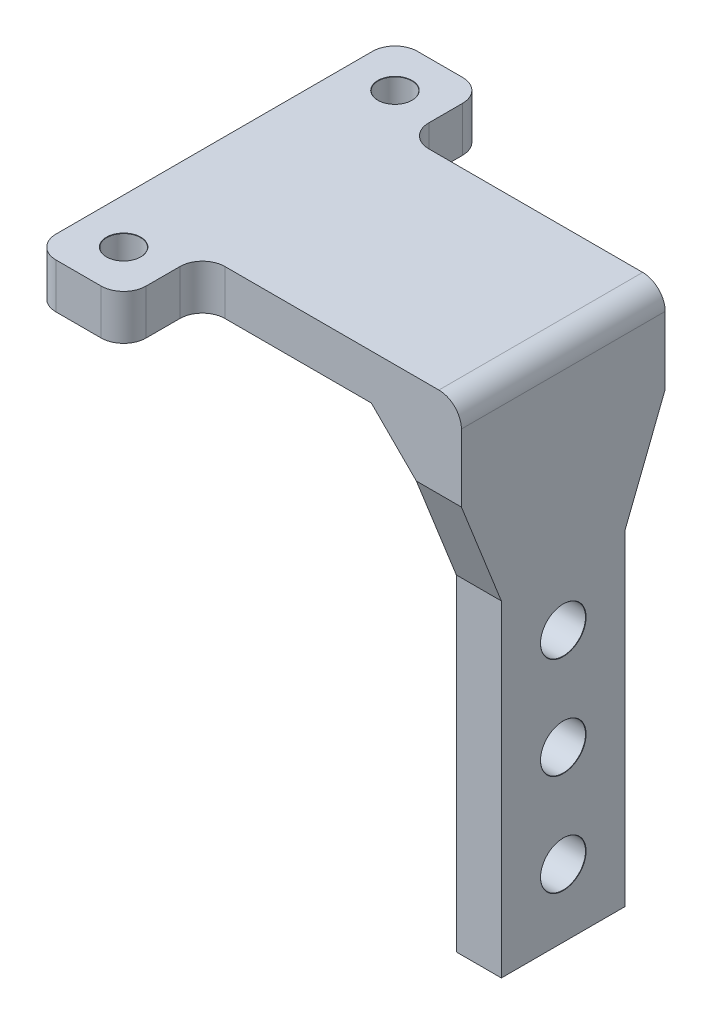
SolidWorks part; units mm, degrees
material "ABS"
ref_plane "Front Plane" through (0, 0, 0) normal (0, 0, 1) x (1, 0, 0)
ref_plane "Top Plane" through (0, 0, 0) normal (0, 1, 0) x (1, 0, 0)
ref_plane "Right Plane" through (0, 0, 0) normal (1, 0, 0) x (0, 0, -1)
sketch "Sketch1" plane through (0, 0, 0) normal (0, 1, 0) x (1, 0, 0)
  line L0 (0, 16.05) -> (0, -16.05)
  line L1 (0, -16.05) -> (8, -16.05)
  line L2 (8, -16.05) -> (8, -9.05)
  line L3 (8, -9.05) -> (31, -9.05)
  line L4 (31, -9.05) -> (31, 9.05)
  line L5 (31, 9.05) -> (8, 9.05)
  line L6 (8, 9.05) -> (8, 16.05)
  line L7 (8, 16.05) -> (0, 16.05)
  dimension "D1" = 32.1
  dimension "D2" = 8
  dimension "D3" = 7
  dimension "D4" = 23
extrude "Boss-Extrude1" add sketch "Sketch1" along normal blind 4
fillet "Fillet1" radius 2 6 edges at (0, 2, -16.05) (8, 2, -9.05) (8, 2, -16.05) (0, 2, 16.05) (8, 2, 16.05) (8, 2, 9.05)
hole_wizard "Ø3.0mm Dowel Hole1" positions "Sketch2" profile "Sketch3" hole size "Ø3.0" standard "ANSI Metric" end condition through all
sketch "Sketch2" plane through (0, 4, 0) normal (0, 1, 0) x (1, 0, 0)
  line L0 (4, 14.9464) -> (4, 9.6271) construction
  line L2 (0, 14.05) -> (0, -14.05) construction
  line L3 (8, 11.05) -> (8, 14.05) construction
  line L4 (6, 16.05) -> (2, 16.05) construction
  line L5 (2, -16.05) -> (6, -16.05) construction
  point P0 (4, 12.05)
  point P2 (4, -12.05)
  dimension "D1" = 4
  dimension "D2" = 4
sketch "Sketch3" plane through (4, 4, -12.05) normal (1, 0, 0) x (0, 0, 1)
  line L0 (0, 0) -> (0, 4)
  line L1 (0, 4) -> (1.5, 4)
  line L2 (1.5, 4) -> (1.5, 0.025)
  line L3 (1.5, 0.025) -> (1.525, 0)
  line L5 (1.525, 0) -> (0, 0)
  line L6 (-1.5, 0.025) -> (-1.525, 0) construction
  line L11 (0, -6.35) -> (0, 107.95) construction
  dimension "Thru Hole Dia." = 3
  dimension "Thru Hole Depth" = 4
  dimension "Near C'Sink Dia." = 3.05
  dimension "Near C'Sink Angle" = 90
sketch "Sketch4" plane through (0, 0, 0) normal (0, -1, 0) x (-1, 0, 0)
  line L0 (-31, 9.05) -> (-10, 9.05) construction
  line L1 (-31, -9.05) -> (-27, -9.05)
  line L2 (-31, -9.05) -> (-31, 9.05)
  line L3 (-31, 9.05) -> (-27, 9.05)
  line L4 (-27, -9.05) -> (-27, 9.05)
  dimension "D1" = 4
extrude "Boss-Extrude2" add sketch "Sketch4" along normal blind 42
chamfer "Chamfer1" distance 4 angle 45 1 edges at (27, 0, 0)
fillet "Fillet2" radius 2 1 edges at (31, 4, 0)
hole_wizard "Ø4.0mm Dowel Hole1" positions "Sketch7" profile "Sketch9" hole size "Ø4.0" standard "ANSI Metric" end condition through all
sketch "Sketch7" plane through (31, 0, 0) normal (1, 0, 0) x (0, 0, -1)
  line L0 (0, -29.3755) -> (0, -38.7068) construction
  line L2 (-9.05, 2) -> (-9.05, -42) construction
  line L3 (9.05, 2) -> (9.05, -42) construction
  line L4 (9.05, -42) -> (-9.05, -42) construction
  point P0 (0, -36)
  point P2 (0, -27)
  point P4 (0, -18)
  dimension "D1" = 6
  dimension "D2" = 9
  dimension "D3" = 9
sketch "Sketch9" plane through (31, -36, 0) normal (0, 1, 0) x (0, 0, -1)
  line L0 (0, 0) -> (0, 31)
  line L1 (0, 31) -> (2, 31)
  line L2 (2, 31) -> (2, 0.025)
  line L3 (2, 0.025) -> (2.025, 0)
  line L5 (2.025, 0) -> (0, 0)
  line L6 (-2, 0.025) -> (-2.025, 0) construction
  line L11 (0, -6.35) -> (0, 107.95) construction
  dimension "Thru Hole Dia." = 4
  dimension "Thru Hole Depth" = 31
  dimension "Near C'Sink Dia." = 4.05
  dimension "Near C'Sink Angle" = 90
sketch "Sketch11" plane through (27, 0, 0) normal (-1, 0, 0) x (0, 0, 1)
  line L0 (-9.05, -4) -> (-5.5, -13)
  line L1 (-5.5, -13) -> (-5.5, -42)
  line L2 (9.05, -42) -> (-9.05, -42) construction
  line L4 (-5.5, -42) -> (-9.05, -42)
  line L5 (-9.05, -4) -> (-9.05, -42)
  line L7 (9.05, -4) -> (-9.05, -4) construction
  dimension "D1" = 9
  dimension "D2" = 3.55
extrude "Cut-Extrude1" cut sketch "Sketch11" against normal through all both and the other way through all
sketch "Sketch12" plane through (27, 0, 0) normal (-1, 0, 0) x (0, 0, 1)
  line L0 (9.05, -4) -> (5.5, -13)
  line L1 (5.5, -13) -> (5.5, -42)
  line L2 (9.05, -42) -> (-5.5, -42) construction
  line L3 (5.5, -42) -> (9.05, -42)
  line L4 (9.05, -42) -> (9.05, -4)
  line L5 (9.05, -4) -> (-9.05, -4) construction
  dimension "D1" = 9
  dimension "D2" = 3.55
extrude "Cut-Extrude2" cut sketch "Sketch12" against normal through all both
